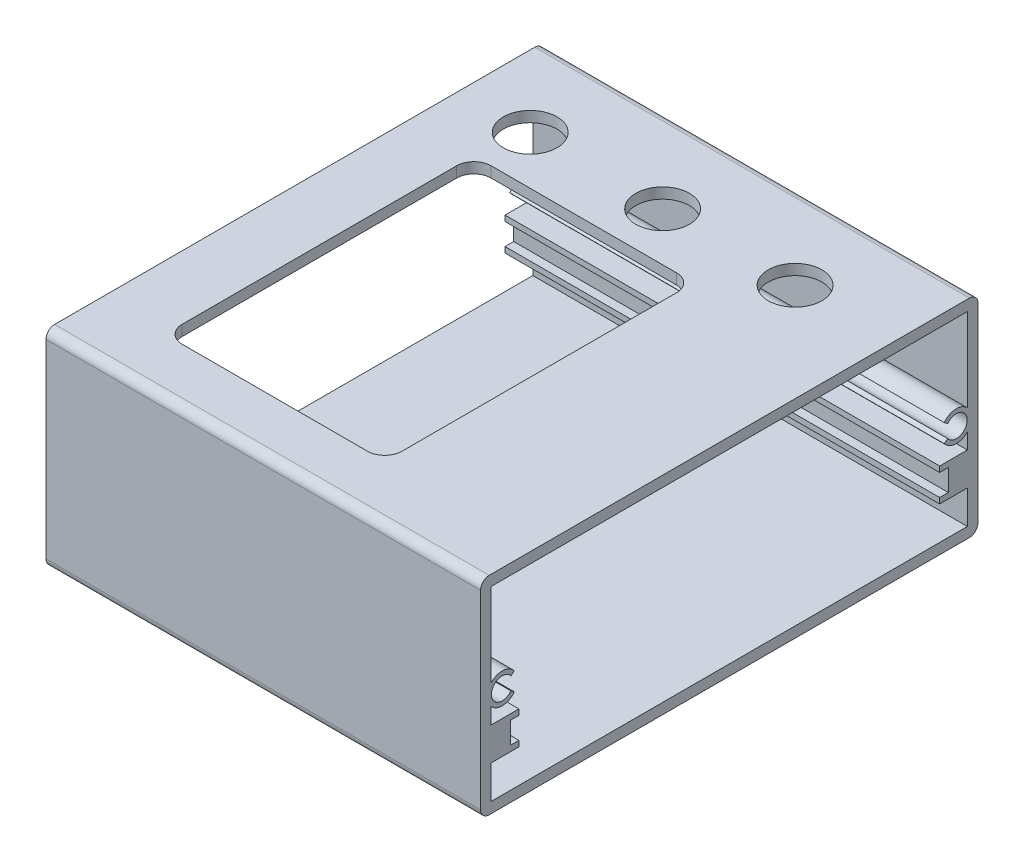
SolidWorks part; units mm, degrees
ref_plane "Front Plane" through (0, 0, 0) normal (0, 0, 1) x (1, 0, 0)
ref_plane "Top Plane" through (0, 0, 0) normal (0, 1, 0) x (1, 0, 0)
ref_plane "Right Plane" through (0, 0, 0) normal (1, 0, 0) x (0, 0, -1)
sketch "Sketch1" plane through (0, 0, 0) normal (1, 0, 0) x (0, 0, -1)
  line L0 (-28.73, 11.98) -> (28.73, 11.98)
  line L1 (-27.5, 10.75) -> (27.5, 10.75)
  line L2 (-27.5, 10.75) -> (-27.5, -10.75)
  line L3 (-27.5, -10.75) -> (27.5, -10.75)
  line L4 (27.5, 10.75) -> (27.5, -10.75)
  line L5 (-27.5, 10.75) -> (27.5, -10.75) construction
  line L6 (-27.5, -10.75) -> (27.5, 10.75) construction
  line L7 (28.73, 11.98) -> (28.73, -11.98)
  line L8 (-28.73, -11.98) -> (28.73, -11.98)
  line L9 (-28.73, 11.98) -> (-28.73, -11.98)
  line L10 (0, 10.75) -> (0, -10.75) construction
  line L11 (-24.3, -5) -> (-27.5, -5) construction
  line L12 (-27.5, -6.9) -> (-24.3, -6.9)
  line L13 (-27.5, -6.9) -> (-27.5, -3.1)
  line L14 (-27.5, -3.1) -> (-24.3, -3.1)
  line L15 (-24.3, -6.9) -> (-24.3, -3.1)
  line L16 (-25.3, -5) -> (-24.3, -5) construction
  line L17 (-24.3, -3.75) -> (-25.3, -3.75)
  line L18 (-24.3, -3.75) -> (-24.3, -6.25)
  line L19 (-24.3, -6.25) -> (-25.3, -6.25)
  line L20 (-25.3, -3.75) -> (-25.3, -6.25)
  line L21 (-25.23, 0.67) -> (-25.23, -0.83)
  line L22 (-25.23, 0.67) -> (-24.83, 0.97)
  line L23 (-25.23, -0.83) -> (-24.83, -1.13)
  line L24 (25.23, 0.67) -> (25.23, -0.83)
  line L25 (27.5, -6.9) -> (24.3, -6.9)
  line L26 (24.3, -6.25) -> (25.3, -6.25)
  line L27 (25.3, -3.75) -> (25.3, -6.25)
  line L28 (24.3, -3.75) -> (25.3, -3.75)
  line L29 (24.3, -6.9) -> (24.3, -3.1)
  line L30 (27.5, -3.1) -> (24.3, -3.1)
  line L31 (25.23, -0.83) -> (24.83, -1.13)
  line L32 (25.23, 0.67) -> (24.83, 0.97)
  circle A0 centre (-26.23, -0.08) radius 1.75
  circle A1 centre (-26.23, -0.08) radius 1.25
  circle A2 centre (26.23, -0.08) radius 1.25
  circle A3 centre (26.23, -0.08) radius 1.75
  point P0 (0, 0)
  dimension "D9" = 3.5
  dimension "D1" = 55
  dimension "D2" = 21.5
  dimension "D4" = 3.85
  dimension "D5" = 3.8
  dimension "D6" = 3.2
  dimension "D7" = 2.5
  dimension "D8" = 1
  dimension "D10" = 2.5
  dimension "D11" = 11.9
  dimension "D12" = 1
  dimension "D3" = 1.23
  dimension "D13" = 0.5
extrude "Boss-Extrude1" add sketch "Sketch1" along normal blind 50.2 contours L0 L9 L8 L7 L4 A3 L3 L2 A0 L1 | A1 L22 A0 L2 L23 | L2 A0 | L20 L17 L15 L14 L2 L12 L19 | A3 L4 | A3 L4 L32 A2 L31 | L4 L30 L29 L28 L27 L26 L25
fillet "Fillet1" radius 1 4 edges at (25.1, -11.98, -28.73) (25.1, 11.98, -28.73) (25.1, -11.98, 28.73) (25.1, 11.98, 28.73)
sketch "Sketch2" plane through (0, 11.98, 0) normal (0, 1, 0) x (1, 0, 0)
  circle A0 centre (38.85, 18.95) radius 3 construction
  circle A1 centre (23.55, 18.95) radius 3 construction
  circle A2 centre (8.25, 18.95) radius 3 construction
  circle A3 centre (8.25, 18.95) radius 3
  circle A4 centre (23.55, 18.95) radius 3
  circle A5 centre (38.85, 18.95) radius 3
  circle A6 centre (8.25, 18.95) radius 3.1
  circle A7 centre (23.55, 18.95) radius 3.1
  circle A8 centre (38.85, 18.95) radius 3.1
  dimension "D1" = 0.1
extrude "Cut-Extrude1" cut sketch "Sketch2" against normal up to next contours A6 A3 | A3 | A7 A4 | A4 | A8 A5 | A5
sketch "Sketch3" plane through (0, 11.98, 0) normal (0, 1, 0) x (1, 0, 0)
  line L0 (9.35, -22.35) -> (30.75, -22.35)
  line L1 (32.75, -20.35) -> (32.75, 11.35)
  line L2 (30.75, 13.35) -> (9.35, 13.35)
  line L3 (7.35, 11.35) -> (7.35, -20.35)
  line L4 (50.2, -27.73) -> (50.2, 27.73)
  line L5 (50.2, 27.73) -> (0, 27.73)
  line L6 (0, 27.73) -> (0, -27.73)
  line L7 (0, -27.73) -> (50.2, -27.73)
  line L8 (50.2, -27.73) -> (50.2, 27.73)
  line L9 (50.2, 27.73) -> (0, 27.73)
  line L10 (0, 27.73) -> (0, -27.73)
  line L11 (0, -27.73) -> (50.2, -27.73)
  line L12 (6.85, 11.35) -> (6.85, -20.35)
  line L13 (30.75, 13.85) -> (9.35, 13.85)
  line L14 (33.25, -20.35) -> (33.25, 11.35)
  line L15 (9.35, -22.85) -> (30.75, -22.85)
  line L16 (6.85, 11.35) -> (6.85, -20.35)
  line L17 (30.75, 13.85) -> (9.35, 13.85)
  line L18 (33.25, -20.35) -> (33.25, 11.35)
  line L19 (9.35, -22.85) -> (30.75, -22.85)
  arc A0 (30.75, -22.35) -> (32.75, -20.35) centre (30.75, -20.35) ccw
  arc A1 (32.75, 11.35) -> (30.75, 13.35) centre (30.75, 11.35) ccw
  arc A2 (9.35, 13.35) -> (7.35, 11.35) centre (9.35, 11.35) ccw
  arc A3 (7.35, -20.35) -> (9.35, -22.35) centre (9.35, -20.35) ccw
  arc A4 (9.35, 13.85) -> (6.85, 11.35) centre (9.35, 11.35) ccw
  arc A5 (33.25, 11.35) -> (30.75, 13.85) centre (30.75, 11.35) ccw
  arc A6 (30.75, -22.85) -> (33.25, -20.35) centre (30.75, -20.35) ccw
  arc A7 (6.85, -20.35) -> (9.35, -22.85) centre (9.35, -20.35) ccw
  arc A8 (9.35, 13.85) -> (6.85, 11.35) centre (9.35, 11.35) ccw
  arc A9 (33.25, 11.35) -> (30.75, 13.85) centre (30.75, 11.35) ccw
  arc A10 (30.75, -22.85) -> (33.25, -20.35) centre (30.75, -20.35) ccw
  arc A11 (6.85, -20.35) -> (9.35, -22.85) centre (9.35, -20.35) ccw
  dimension "D1" = 0
  dimension "D2" = 0
  dimension "D3" = 0.5
extrude "Cut-Extrude2" cut sketch "Sketch3" against normal up to next contours L3 A3 L0 A0 L1 A1 L2 A2
